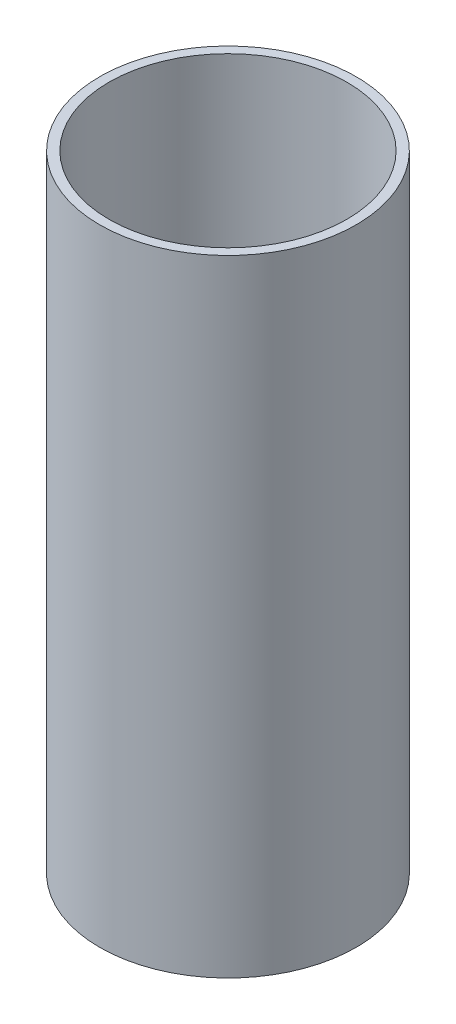
SolidWorks part; units mm, degrees
ref_plane "Front Plane" through (0, 0, 0) normal (0, 0, 1) x (1, 0, 0)
ref_plane "Top Plane" through (0, 0, 0) normal (0, 1, 0) x (1, 0, 0)
ref_plane "Right Plane" through (0, 0, 0) normal (1, 0, 0) x (0, 0, -1)
sketch "Sketch1" plane through (0, 0, 0) normal (0, 1, 0) x (1, 0, 0)
  circle A0 centre (0, 0) radius 19
  circle A1 centre (0, 0) radius 20.5
  dimension "D1" = 38
  dimension "D2" = 1.5
extrude "Boss-Extrude1" add sketch "Sketch1" along normal blind 100
